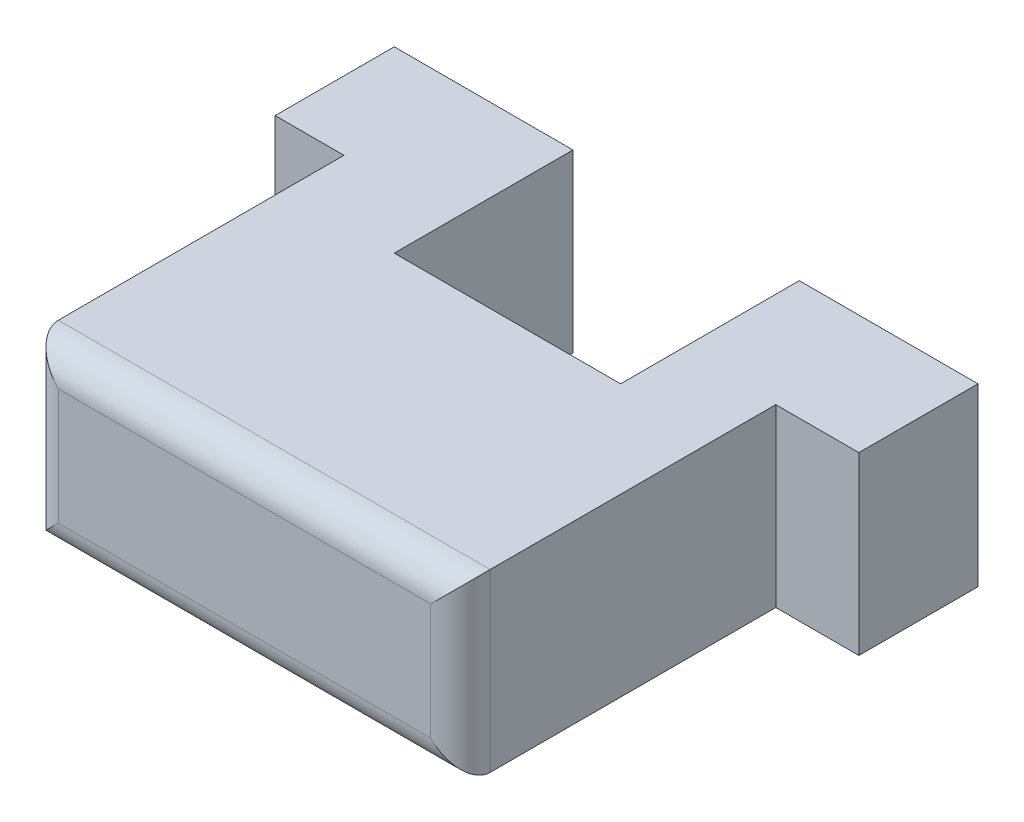
SolidWorks part; units mm, degrees
ref_plane "Front Plane" through (0, 0, 0) normal (0, 0, 1) x (1, 0, 0)
ref_plane "Top Plane" through (0, 0, 0) normal (0, 1, 0) x (1, 0, 0)
ref_plane "Right Plane" through (0, 0, 0) normal (1, 0, 0) x (0, 0, -1)
sketch "Sketch1" plane through (0, 0, 0) normal (0, 0, 1) x (1, 0, 0)
  line L1 (-7.25, 2.95) -> (7.25, 2.95)
  line L2 (-7.25, 2.95) -> (-7.25, -2.95)
  line L3 (-7.25, -2.95) -> (7.25, -2.95)
  line L4 (7.25, 2.95) -> (7.25, -2.95)
  line L5 (-7.25, 2.95) -> (7.25, -2.95) construction
  line L6 (-7.25, -2.95) -> (7.25, 2.95) construction
  point P0 (0, 0)
  dimension "D1" = 14.5
  dimension "D2" = 5.9
extrude "Boss-Extrude1" add sketch "Sketch1" along normal blind 2.59 contours L1 L4 L3 L2
sketch "Sketch2" plane through (0, 0, 0) normal (0, 0, -1) x (-1, 0, 0)
  line L0 (3.5601, 2.95) -> (7.25, 2.95)
  line L1 (7.25, 2.95) -> (-7.25, 2.95) construction
  line L2 (-7.25, 2.95) -> (-4.0399, 2.95)
  line L3 (-7.25, 2.95) -> (-7.25, -2.95)
  line L4 (-7.25, -2.95) -> (-4.0399, -2.95)
  line L5 (-4.0399, 2.95) -> (-4.0399, -2.95)
  line L6 (7.25, -2.95) -> (-7.25, -2.95) construction
  line L7 (7.25, 2.95) -> (7.25, -2.95)
  line L8 (7.25, -2.95) -> (3.5601, -2.95)
  line L9 (-7.25, 2.95) -> (-7.25, -2.95) construction
  line L10 (3.4101, 3.625) -> (3.4101, -3.925) construction
  line L12 (3.5601, 2.95) -> (3.5601, -2.95)
  line L16 (-3.8899, 3.625) -> (-3.8899, -3.925) construction
  dimension "D1" = 0.15
  dimension "D2" = 0.15
  dimension "D3" = 0
extrude "Boss-Extrude2" add sketch "Sketch2" along normal blind 2
sketch "Sketch5" plane through (0, 0, -2) normal (0, 0, -1) x (-1, 0, 0)
  line L1 (-4.0399, 2.95) -> (-10.0399, 2.95)
  line L2 (-4.0399, 2.95) -> (-4.0399, -2.95)
  line L3 (-4.0399, -2.95) -> (-10.0399, -2.95)
  line L4 (-10.0399, 2.95) -> (-10.0399, -2.95)
  line L5 (3.5601, 2.95) -> (9.5601, 2.95)
  line L6 (3.5601, 2.95) -> (3.5601, -2.95)
  line L7 (3.5601, -2.95) -> (9.5601, -2.95)
  line L8 (9.5601, 2.95) -> (9.5601, -2.95)
  dimension "D1" = 6
  dimension "D2" = 6
extrude "Boss-Extrude3" add sketch "Sketch5" along normal blind 4
sketch "Sketch7" plane through (0, 0, 2.59) normal (0, 0, 1) x (1, 0, 0)
  line L4 (-7.25, 2.95) -> (-7.25, -2.95)
  line L5 (-7.25, -2.95) -> (7.25, -2.95)
  line L6 (7.25, -2.95) -> (7.25, 2.95)
  line L7 (7.25, 2.95) -> (-7.25, 2.95)
  line L8 (-7.25, 2.95) -> (-7.25, -2.95)
  line L9 (-7.25, -2.95) -> (7.25, -2.95)
  line L10 (7.25, -2.95) -> (7.25, 2.95)
  line L11 (7.25, 2.95) -> (-7.25, 2.95)
  dimension "D1" = 0
extrude "Boss-Extrude5" add sketch "Sketch7" along normal blind 6
fillet "Fillet2" radius 1 4 edges at (0, 2.95, 8.59) (-7.25, 0, 8.59) (0, -2.95, 8.59) (7.25, 0, 8.59)
